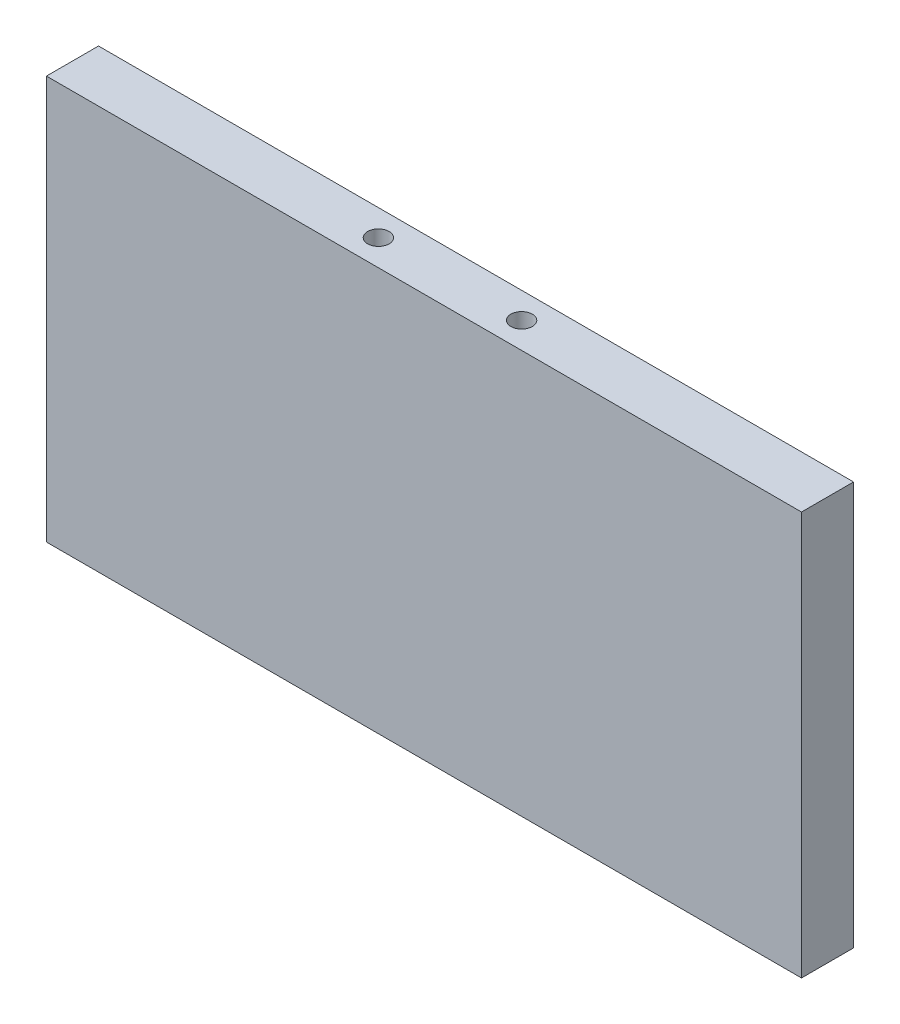
SolidWorks part; units mm, degrees
ref_plane "Front" through (0, 0, 0) normal (0, 0, 1) x (1, 0, 0)
ref_plane "Top" through (0, 0, 0) normal (0, 1, 0) x (1, 0, 0)
ref_plane "Right" through (0, 0, 0) normal (1, 0, 0) x (0, 0, -1)
sketch "Esquisse1" plane through (0, 0, 0) normal (0, 0, 1) x (1, 0, 0)
  line L1 (0, 0) -> (116, 0)
  line L2 (0, 0) -> (0, 62)
  line L3 (0, 62) -> (116, 62)
  line L4 (116, 0) -> (116, 62)
  dimension "D1" = 116
  dimension "D2" = 62
extrude "Boss.-Extru.1" add sketch "Esquisse1" along normal blind 8
sketch "Esquisse2" plane through (0, 62, 0) normal (0, 1, 0) x (1, 0, 0)
  line L0 (58, -8) -> (58, 0) construction
  line L1 (116, -8) -> (0, -8) construction
  line L2 (116, 0) -> (0, 0) construction
  line L3 (58, -4) -> (47, -4) construction
  circle A0 centre (47, -4) radius 1.65
  circle A1 centre (69, -4) radius 1.65
  dimension "D1" = 3.3
  dimension "D2" = 22
extrude "Enlèv. mat.-Extru.1" cut sketch "Esquisse2" against normal blind 10
